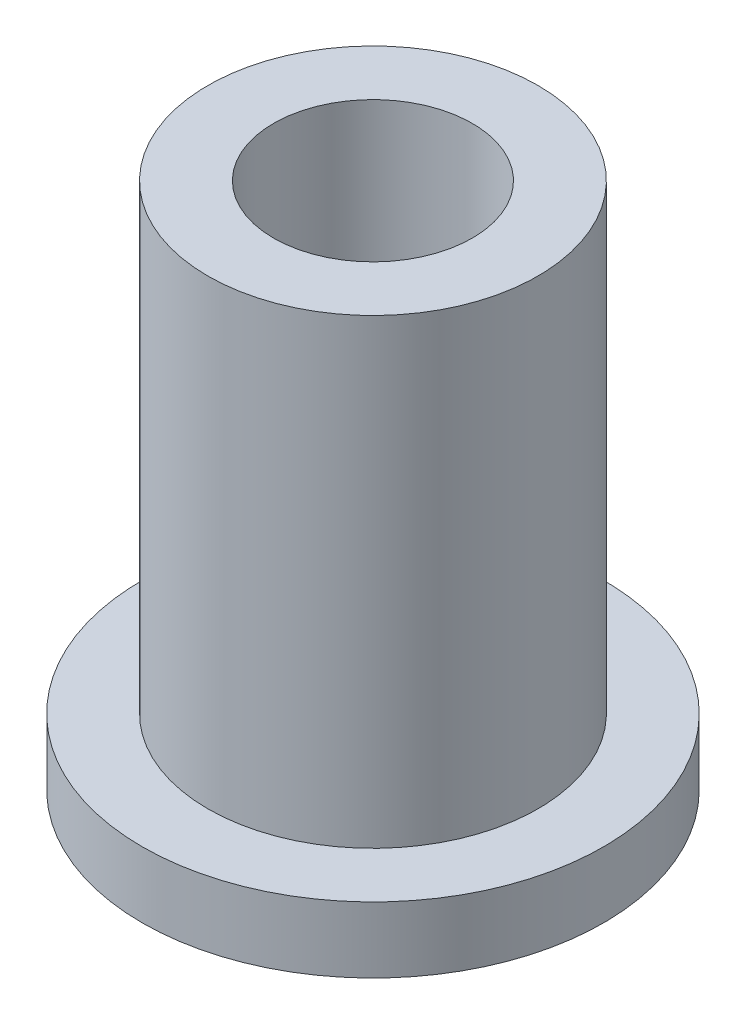
SolidWorks part; units mm, degrees
ref_plane "Front" through (0, 0, 0) normal (0, 0, 1) x (1, 0, 0)
ref_plane "Top" through (0, 0, 0) normal (0, 1, 0) x (1, 0, 0)
ref_plane "Right" through (0, 0, 0) normal (1, 0, 0) x (0, 0, -1)
sketch "Sketch1" plane through (0, 0, 0) normal (0, 1, 0) x (1, 0, 0)
  circle A0 centre (0, 0) radius 2.394
  circle A1 centre (0, 0) radius 3.9751
  circle A2 centre (0, 0) radius 5.5562
  dimension "ID" = 4.7879
  dimension "OD" = 7.9502
  dimension "FlangeOD" = 11.1125
sketch "Sketch2" plane through (0, 0, 0) normal (0, 1, 0) x (1, 0, 0)
  circle A0 centre (0, 0) radius 2.394 construction
  circle A1 centre (0, 0) radius 3.9751 construction
  circle A2 centre (0, 0) radius 2.394
  circle A3 centre (0, 0) radius 3.9751
extrude "Boss-Extrude1" add sketch "Sketch2" along normal blind 12.7
sketch "Sketch3" plane through (0, 0, 0) normal (0, 1, 0) x (1, 0, 0)
  circle A0 centre (0, 0) radius 5.5562 construction
  circle A1 centre (0, 0) radius 3.9751 construction
  circle A2 centre (0, 0) radius 5.5562
  circle A3 centre (0, 0) radius 3.9751
extrude "Boss-Extrude2" add sketch "Sketch3" along normal blind 1.5875
